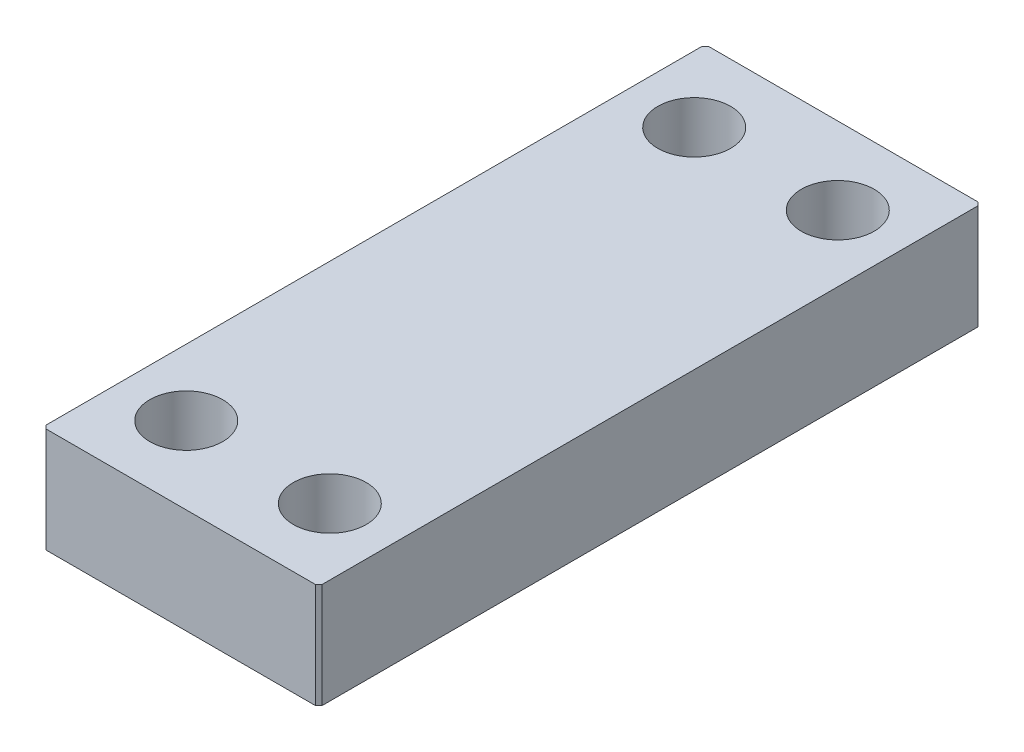
SolidWorks part; units mm, degrees
ref_plane "Front Plane" through (0, 0, 0) normal (0, 0, 1) x (1, 0, 0)
ref_plane "Top Plane" through (0, 0, 0) normal (0, 1, 0) x (1, 0, 0)
ref_plane "Right Plane" through (0, 0, 0) normal (1, 0, 0) x (0, 0, -1)
sketch "Sketch1" plane through (0, 0, 0) normal (0, 1, 0) x (1, 0, 0)
  line L1 (12.5, 30) -> (-12.5, 30)
  line L2 (12.5, 30) -> (12.5, -30)
  line L3 (12.5, -30) -> (-12.5, -30)
  line L4 (-12.5, 30) -> (-12.5, -30)
  line L5 (12.5, 30) -> (-12.5, -30) construction
  line L6 (12.5, -30) -> (-12.5, 30) construction
  line L7 (6.5, -23) -> (-6.5, -23) construction
  line L8 (6.5, -23) -> (6.5, 23) construction
  line L9 (6.5, 23) -> (-6.5, 23) construction
  line L10 (-6.5, -23) -> (-6.5, 23) construction
  line L11 (6.5, -23) -> (-6.5, 23) construction
  line L12 (6.5, 23) -> (-6.5, -23) construction
  circle A0 centre (6.5, 23) radius 3.3
  circle A1 centre (6.5, -23) radius 3.3
  circle A2 centre (-6.5, 23) radius 3.3
  circle A3 centre (-6.5, -23) radius 3.3
  point P0 (0, 0)
  point P12 (0, 0)
  dimension "D4" = 6.6
  dimension "D1" = 25
  dimension "D2" = 60
  dimension "D3" = 46
  dimension "D5" = 13
extrude "Boss-Extrude1" add sketch "Sketch1" along normal blind 9.5
chamfer "Chamfer1" distance 0.3 angle 45 4 edges at (12.5, 4.75, -30) (-12.5, 4.75, -30) (-12.5, 4.75, 30) (12.5, 4.75, 30)
